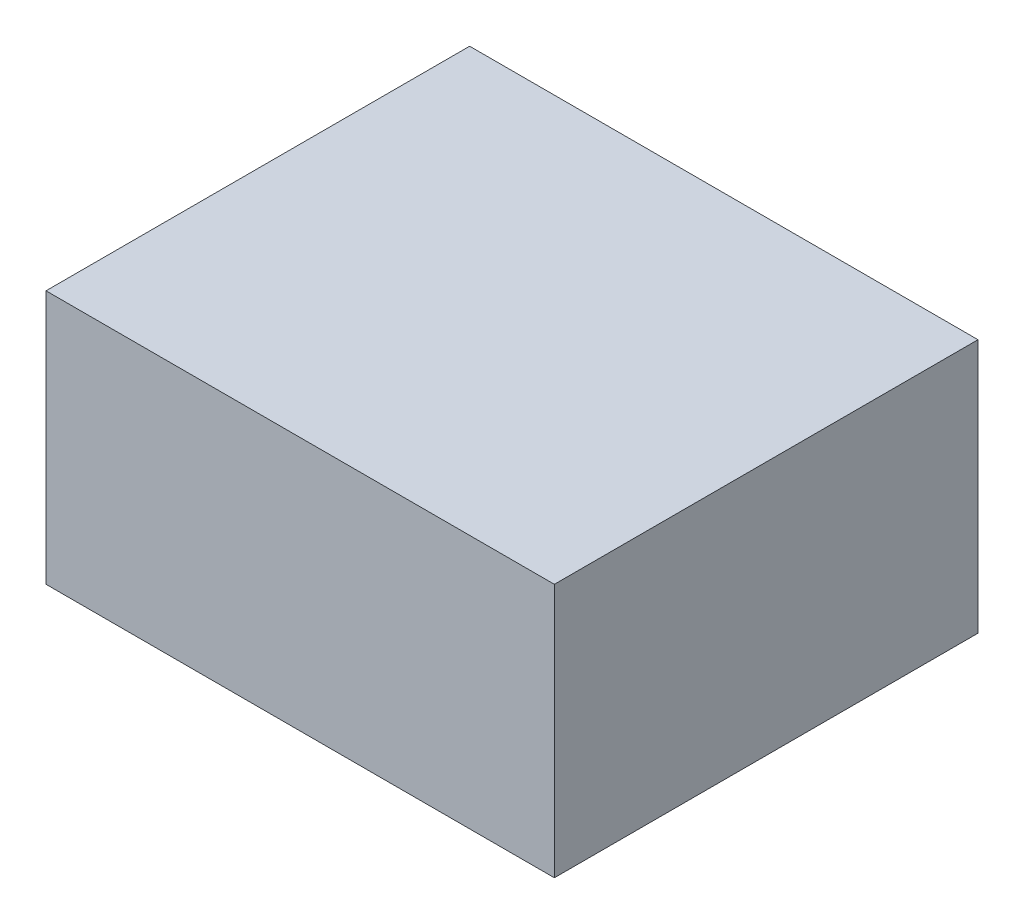
SolidWorks part; units mm, degrees
ref_plane "Front Plane" through (0, 0, 0) normal (0, 0, 1) x (1, 0, 0)
ref_plane "Top Plane" through (0, 0, 0) normal (0, 1, 0) x (1, 0, 0)
ref_plane "Right Plane" through (0, 0, 0) normal (1, 0, 0) x (0, 0, -1)
sketch "Sketch1" plane through (0, 0, 0) normal (0, 1, 0) x (1, 0, 0)
  line L1 (0, 0) -> (36, 0)
  line L2 (0, 0) -> (0, 30)
  line L3 (0, 30) -> (36, 30)
  line L4 (36, 0) -> (36, 30)
  dimension "D1" = 36
  dimension "D2" = 30
extrude "Boss-Extrude1" add sketch "Sketch1" along normal blind 18 contours L2 L1 L4 L3
